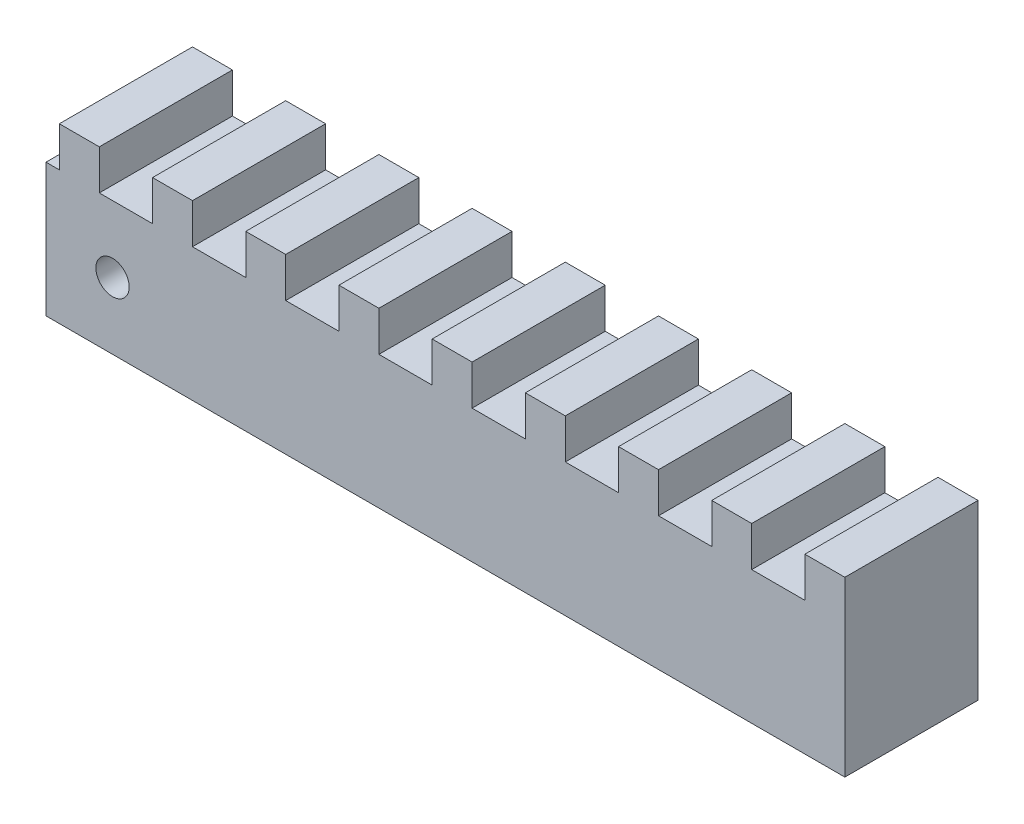
SolidWorks part; units mm, degrees
ref_plane "Front Plane" through (0, 0, 0) normal (0, 0, 1) x (1, 0, 0)
ref_plane "Top Plane" through (0, 0, 0) normal (0, 1, 0) x (1, 0, 0)
ref_plane "Right Plane" through (0, 0, 0) normal (1, 0, 0) x (0, 0, -1)
ref_plane "Plane4"
sketch "Sketch1" plane through (0, 0, 0) normal (0, 0, 1) x (1, 0, 0)
  line L0 (152.4, 25.4) -> (152.4, 33.02)
  line L1 (152.4, 33.02) -> (144.7674, 33.02)
  line L2 (144.7674, 33.02) -> (144.7674, 25.4)
  line L3 (144.7674, 25.4) -> (134.6269, 25.4)
  line L4 (134.6269, 25.4) -> (134.6269, 33.02)
  line L5 (134.6269, 33.02) -> (127.0069, 33.02)
  line L6 (127.0069, 33.02) -> (127.0069, 25.4)
  line L7 (127.0069, 25.4) -> (116.8469, 25.4)
  line L8 (116.8469, 25.4) -> (116.8469, 33.02)
  line L9 (116.8469, 33.02) -> (109.2269, 33.02)
  line L10 (109.2269, 33.02) -> (109.2269, 25.4)
  line L11 (109.2269, 25.4) -> (99.0669, 25.4)
  line L12 (99.0669, 25.4) -> (99.0669, 33.02)
  line L13 (99.0669, 33.02) -> (91.4469, 33.02)
  line L14 (91.4469, 33.02) -> (91.4469, 25.4)
  line L15 (91.4469, 25.4) -> (81.2869, 25.4)
  line L16 (81.2869, 25.4) -> (81.2869, 33.02)
  line L17 (81.2869, 33.02) -> (73.6669, 33.02)
  line L18 (73.6669, 33.02) -> (73.6669, 25.4)
  line L19 (73.6669, 25.4) -> (63.5069, 25.4)
  line L20 (63.5069, 25.4) -> (63.5069, 33.02)
  line L21 (63.5069, 33.02) -> (55.8869, 33.02)
  line L22 (55.8869, 33.02) -> (55.8869, 25.4)
  line L23 (55.8869, 25.4) -> (45.7269, 25.4)
  line L24 (45.7269, 25.4) -> (45.7269, 33.02)
  line L25 (45.7269, 33.02) -> (38.1069, 33.02)
  line L26 (38.1069, 33.02) -> (38.1069, 25.4)
  line L27 (38.1069, 25.4) -> (27.9469, 25.4)
  line L28 (27.9469, 25.4) -> (27.9469, 33.02)
  line L29 (27.9469, 33.02) -> (20.3269, 33.02)
  line L30 (20.3269, 33.02) -> (20.3269, 25.4)
  line L31 (20.3269, 25.4) -> (10.1669, 25.4)
  line L32 (10.1669, 25.4) -> (10.1669, 33.02)
  line L33 (10.1669, 33.02) -> (2.5469, 33.02)
  line L34 (2.5469, 33.02) -> (2.5469, 25.4)
  line L35 (2.5469, 25.4) -> (0, 25.4)
  line L36 (0, 25.4) -> (0, 0)
  line L37 (0, 0) -> (152.4, 0)
  line L38 (152.4, 0) -> (152.4, 25.4)
  circle A0 centre (12.6947, 12.7) radius 3.175
  dimension "D2" = 6.35
  dimension "D1" = 25.4
  dimension "D3" = 7.62
  dimension "D4" = 7.62
  dimension "D5" = 7.62
  dimension "D6" = 7.62
  dimension "D7" = 7.62
  dimension "D8" = 7.62
  dimension "D9" = 7.62
  dimension "D10" = 7.62
  dimension "D11" = 7.62
  dimension "D12" = 7.62
  dimension "D13" = 7.62
  dimension "D14" = 7.62
  dimension "D15" = 7.62
  dimension "D16" = 10.16
  dimension "D17" = 10.16
  dimension "D18" = 10.16
  dimension "D19" = 10.16
  dimension "D20" = 10.16
  dimension "D21" = 10.16
  dimension "D22" = 7.62
  dimension "D23" = 7.62
  dimension "D24" = 10.16
extrude "Extrusion2" add sketch "Sketch1" along normal blind 25.4 contours L37 L38 L0 L1 L2 L3 L4 L5 L6 L7 L8 L9 L10 L11 L12 L13 L14 L15 L16 L17 L18 L19 L20 L21 L22 L23 L24 L25 L26 L27 L28 L29 L30 L31 L32 L33 L34 L35 L36 A0
